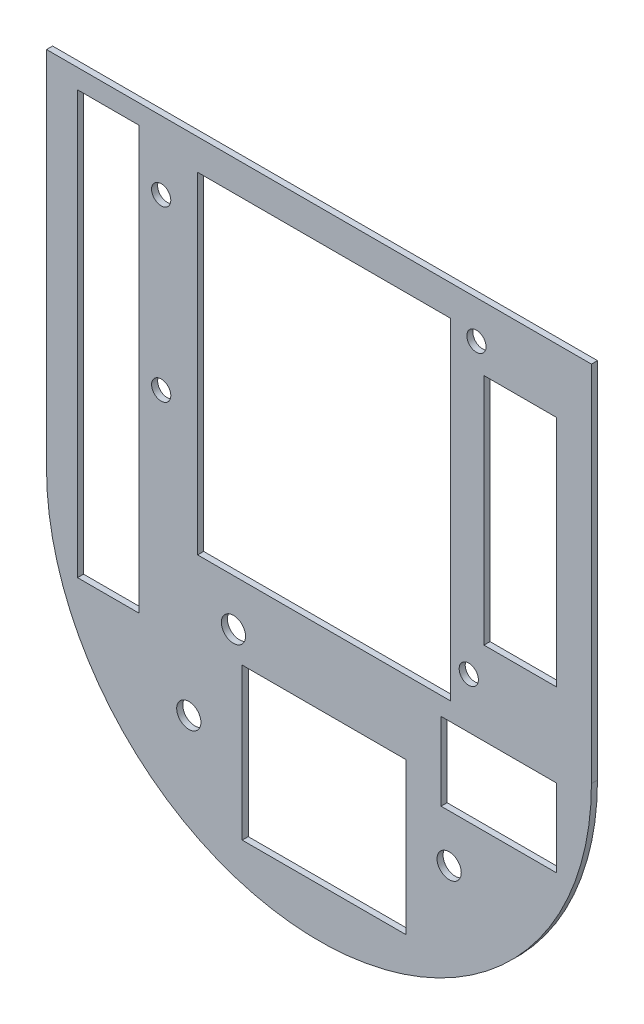
SolidWorks part; units mm, degrees
material "ABS"
ref_plane "Front Plane" through (0, 0, 0) normal (0, 0, 1) x (1, 0, 0)
ref_plane "Top Plane" through (0, 0, 0) normal (0, 1, 0) x (1, 0, 0)
ref_plane "Right Plane" through (0, 0, 0) normal (1, 0, 0) x (0, 0, -1)
sketch "Sketch1" plane through (0, 0, 0) normal (0, 0, 1) x (1, 0, 0)
  line L0 (61.11, 41.9357) -> (61.11, -18.0643)
  line L1 (-28.89, 41.9357) -> (-28.89, -18.0643)
  line L2 (61.11, 41.9357) -> (-28.89, 41.9357)
  line L3 (-28.89, -18.0643) -> (61.11, -18.0643) construction
  line L4 (16.11, -18.0643) -> (16.11, 41.9357) construction
  circle A0 centre (37.61, -41.5643) radius 2
  circle A1 centre (-5.39, -41.5643) radius 2
  circle A2 centre (1.985, -25.5643) radius 2
  circle A3 centre (-9.95, 2.6918) radius 1.5875
  circle A4 centre (40.85, -12.5482) radius 1.5875
  circle A5 centre (42.12, 35.7118) radius 1.5875
  circle A6 centre (-9.95, 30.6318) radius 1.5875
  arc A7 (-28.89, -18.0643) -> (61.11, -18.0643) centre (16.11, -18.0643) ccw
extrude "Boss-Extrude1" add sketch "Sketch1" along normal blind 1
sketch "Sketch2" plane through (0, 0, 1) normal (0, 0, 1) x (1, 0, 0)
  line L1 (37.8244, -17.8763) -> (-3.9303, -17.8763)
  line L2 (37.8244, -17.8763) -> (37.8244, 36.853)
  line L3 (37.8244, 36.853) -> (-3.9303, 36.853)
  line L4 (-3.9303, -17.8763) -> (-3.9303, 36.853)
  line L5 (37.8244, -17.8763) -> (-3.9303, 36.853) construction
  line L6 (37.8244, 36.853) -> (-3.9303, -17.8763) construction
  line L7 (-23.7737, -31.0485) -> (-13.5812, -31.0485)
  line L8 (-23.7737, -31.0485) -> (-23.7737, 38.7364)
  line L9 (-23.7737, 38.7364) -> (-13.5812, 38.7364)
  line L10 (-13.5812, -31.0485) -> (-13.5812, 38.7364)
  line L11 (-23.7737, -31.0485) -> (-13.5812, 38.7364) construction
  line L12 (-23.7737, 38.7364) -> (-13.5812, -31.0485) construction
  line L13 (30.4632, -54.9903) -> (3.4309, -54.9903)
  line L14 (30.4632, -54.9903) -> (30.4632, -29.9522)
  line L15 (30.4632, -29.9522) -> (3.4309, -29.9522)
  line L16 (3.4309, -54.9903) -> (3.4309, -29.9522)
  line L17 (30.4632, -54.9903) -> (3.4309, -29.9522) construction
  line L18 (30.4632, -29.9522) -> (3.4309, -54.9903) construction
  line L19 (43.3638, -7.1298) -> (55.3289, -7.1298)
  line L20 (43.3638, -7.1298) -> (43.3638, 31.4244)
  line L21 (43.3638, 31.4244) -> (55.3289, 31.4244)
  line L22 (55.3289, -7.1298) -> (55.3289, 31.4244)
  line L23 (43.3638, -7.1298) -> (55.3289, 31.4244) construction
  line L24 (43.3638, 31.4244) -> (55.3289, -7.1298) construction
  line L25 (36.2734, -33.719) -> (55.3289, -33.719)
  line L26 (36.2734, -33.719) -> (36.2734, -20.8676)
  line L27 (36.2734, -20.8676) -> (55.3289, -20.8676)
  line L28 (55.3289, -33.719) -> (55.3289, -20.8676)
  line L29 (36.2734, -33.719) -> (55.3289, -20.8676) construction
  line L30 (36.2734, -20.8676) -> (55.3289, -33.719) construction
  point P0 (16.9471, 9.4883)
  point P6 (16.9471, -42.4712)
  point P7 (-18.6774, 3.8439)
  point P16 (49.3464, 12.1473)
  point P21 (45.8012, -27.2933)
extrude "Cut-Extrude1" cut sketch "Sketch2" against normal through all
